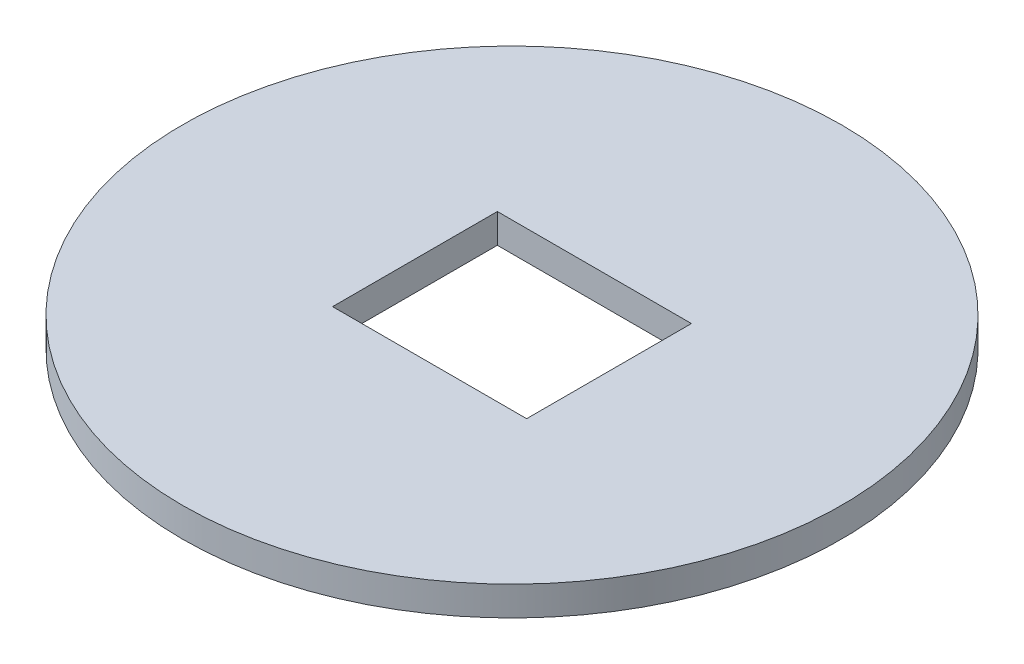
SolidWorks part; units mm, degrees
material "AISI 304"
ref_plane "前视基准面" through (0, 0, 0) normal (0, 0, 1) x (1, 0, 0)
ref_plane "上视基准面" through (0, 0, 0) normal (0, 1, 0) x (1, 0, 0)
ref_plane "右视基准面" through (0, 0, 0) normal (1, 0, 0) x (0, 0, -1)
sketch "Sketch2" plane through (0, 0, 0) normal (0, 1, 0) x (1, 0, 0)
  line L1 (-26.5, 22.5) -> (26.5, 22.5)
  line L2 (-26.5, 22.5) -> (-26.5, -22.5)
  line L3 (-26.5, -22.5) -> (26.5, -22.5)
  line L4 (26.5, 22.5) -> (26.5, -22.5)
  circle A0 centre (0, 0) radius 90
  point P7 (-26.5, 0)
  point P10 (0, 22.5)
  dimension "D1" = 45
  dimension "D2" = 53
extrude "Extrude1" add sketch "Sketch2" along normal blind 8
sketch "Sketch3" plane through (0, 0, 0) normal (0, -1, 0) x (1, 0, 0)
  line L1 (-27.5, 27.5) -> (27.5, 27.5)
  line L2 (-27.5, 27.5) -> (-27.5, -27.5)
  line L3 (-27.5, -27.5) -> (27.5, -27.5)
  line L4 (27.5, 27.5) -> (27.5, -27.5)
  point P4 (0, 27.5)
  point P6 (27.5, 0)
extrude "Extrude2" [suppressed] add sketch "Sketch3" along normal blind 60
shell "Shell2" [suppressed] thickness 2.5
sketch "Sketch5" plane through (0, 0, 0) normal (0, -1, 0) x (1, 0, 0)
  line L1 (-26.2714, 80.9883) -> (-23.2714, 80.9883)
  line L2 (-26.2714, 80.9883) -> (-26.2714, 40.9883)
  line L3 (-26.2714, 40.9883) -> (-23.2714, 40.9883)
  line L4 (-23.2714, 80.9883) -> (-23.2714, 40.9883)
extrude "Extrude4" [suppressed] add sketch "Sketch5" along normal blind 35
pattern_linear "LPattern1" [suppressed] count 6 spacing 10
sketch "Sketch6" plane through (0, 0, 0) normal (0, 0, 1) x (1, 0, 0)
  line L0 (0, 0) -> (0, 47.4008) construction
pattern_circular "CirPattern1" [suppressed] count 4 every 90 about axis through (0, 0, 0) along (0, 1, 0)
